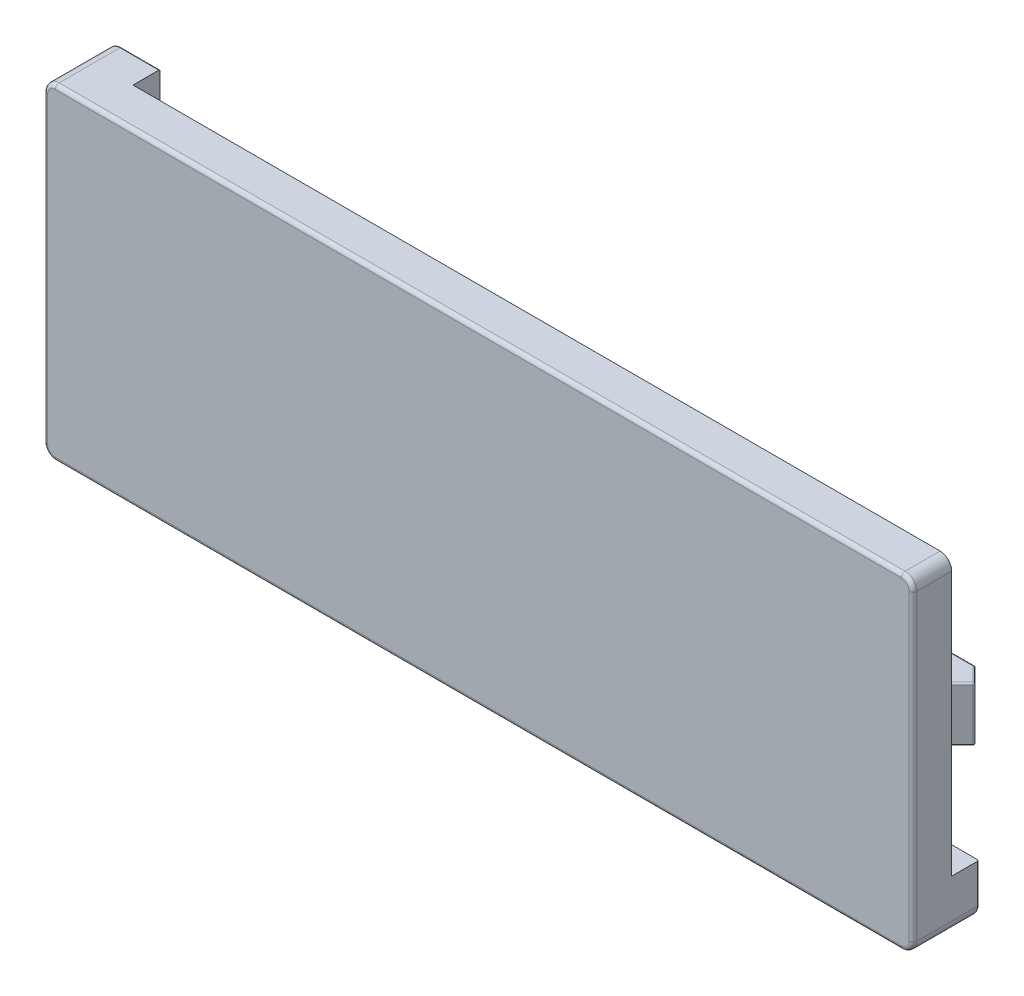
SolidWorks part; units mm, degrees
ref_plane "Front Plane" through (0, 0, 0) normal (0, 0, 1) x (1, 0, 0)
ref_plane "Top Plane" through (0, 0, 0) normal (0, 1, 0) x (1, 0, 0)
ref_plane "Right Plane" through (0, 0, 0) normal (1, 0, 0) x (0, 0, -1)
sketch "Sketch1" plane through (0, 0, 0) normal (0, 0, 1) x (1, 0, 0)
  line L1 (55.95, -21) -> (-55.95, -21)
  line L2 (55.95, -21) -> (55.95, 21)
  line L3 (55.95, 21) -> (-55.95, 21)
  line L4 (-55.95, -21) -> (-55.95, 21)
  line L5 (55.95, -21) -> (-55.95, 21) construction
  line L6 (55.95, 21) -> (-55.95, -21) construction
  point P0 (0, 0)
  dimension "D1" = 111.9
  dimension "D2" = 42
extrude "Boss-Extrude1" add sketch "Sketch1" along normal blind 5
sketch "Sketch2" plane through (0, 0, 0) normal (0, 0, -1) x (-1, 0, 0)
  line L1 (55.95, 21) -> (49.45, 21)
  line L2 (55.95, 21) -> (55.95, 14.5)
  line L3 (55.95, 14.5) -> (49.45, 14.5)
  line L4 (49.45, 21) -> (49.45, 14.5)
  line L5 (-55.95, -21) -> (-49.45, -21)
  line L6 (-55.95, -21) -> (-55.95, -14.5)
  line L7 (-55.95, -14.5) -> (-49.45, -14.5)
  line L8 (-49.45, -21) -> (-49.45, -14.5)
  dimension "D1" = 6.5
  dimension "D2" = 6.5
extrude "Boss-Extrude2" add sketch "Sketch2" along normal blind 3.5
sketch "Sketch3" plane through (0, 0, 0) normal (0, 0, -1) x (-1, 0, 0)
  line L0 (-45.45, -17) -> (51.95, -17)
  line L1 (51.95, -17) -> (51.95, 10.5)
  line L2 (51.95, 10.5) -> (45.45, 10.5)
  line L3 (45.45, 10.5) -> (45.45, 17)
  line L4 (45.45, 17) -> (-51.95, 17)
  line L5 (-51.95, 17) -> (-51.95, -10.5)
  line L6 (-51.95, -10.5) -> (-45.45, -10.5)
  line L7 (-45.45, -10.5) -> (-45.45, -17)
  line L8 (-49.45, -14.5) -> (-49.45, -21)
  line L9 (-49.45, -21) -> (55.95, -21)
  line L10 (55.95, -21) -> (55.95, 14.5)
  line L11 (55.95, 14.5) -> (49.45, 14.5)
  line L12 (49.45, 14.5) -> (49.45, 21)
  line L13 (49.45, 21) -> (-55.95, 21)
  line L14 (-55.95, 21) -> (-55.95, -14.5)
  line L15 (-55.95, -14.5) -> (-49.45, -14.5)
  line L16 (-49.45, -14.5) -> (-49.45, -21) construction
  line L17 (-49.45, -21) -> (55.95, -21) construction
  line L18 (55.95, -21) -> (55.95, 14.5) construction
  line L19 (55.95, 14.5) -> (49.45, 14.5) construction
  line L20 (49.45, 14.5) -> (49.45, 21) construction
  line L21 (49.45, 21) -> (-55.95, 21) construction
  line L22 (-55.95, 21) -> (-55.95, -14.5) construction
  line L23 (-55.95, -14.5) -> (-49.45, -14.5) construction
  line L24 (-42.45, -14) -> (48.95, -14)
  line L25 (48.95, -14) -> (48.95, 7.5)
  line L26 (48.95, 7.5) -> (42.45, 7.5)
  line L27 (42.45, 7.5) -> (42.45, 14)
  line L28 (42.45, 14) -> (-48.95, 14)
  line L29 (-48.95, 14) -> (-48.95, -7.5)
  line L30 (-48.95, -7.5) -> (-42.45, -7.5)
  line L31 (-42.45, -7.5) -> (-42.45, -14)
  dimension "D1" = 0
  dimension "D2" = 4
  dimension "D3" = 3
extrude "Cut-Extrude1" cut sketch "Sketch3" against normal blind 2
sketch "Sketch5" plane through (0, 0, 0) normal (0, 0, -1) x (-1, 0, 0)
  line L0 (-40.45, -12) -> (46.95, -12)
  line L1 (46.95, -12) -> (46.95, 5.5)
  line L2 (46.95, 5.5) -> (40.45, 5.5)
  line L3 (40.45, 5.5) -> (40.45, 12)
  line L4 (40.45, 12) -> (-46.95, 12)
  line L5 (-46.95, 12) -> (-46.95, -5.5)
  line L6 (-46.95, -5.5) -> (-40.45, -5.5)
  line L7 (-40.45, -5.5) -> (-40.45, -12)
  line L8 (-42.45, -7.5) -> (-42.45, -14)
  line L9 (-42.45, -14) -> (48.95, -14)
  line L10 (48.95, -14) -> (48.95, 7.5)
  line L11 (48.95, 7.5) -> (42.45, 7.5)
  line L12 (42.45, 7.5) -> (42.45, 14)
  line L13 (42.45, 14) -> (-48.95, 14)
  line L14 (-48.95, 14) -> (-48.95, -7.5)
  line L15 (-48.95, -7.5) -> (-42.45, -7.5)
  line L16 (-42.45, -7.5) -> (-42.45, -14)
  line L17 (-42.45, -14) -> (48.95, -14)
  line L18 (48.95, -14) -> (48.95, 7.5)
  line L19 (48.95, 7.5) -> (42.45, 7.5)
  line L20 (42.45, 7.5) -> (42.45, 14)
  line L21 (42.45, 14) -> (-48.95, 14)
  line L22 (-48.95, 14) -> (-48.95, -7.5)
  line L23 (-48.95, -7.5) -> (-42.45, -7.5)
  dimension "D1" = 0
  dimension "D2" = 2
extrude "Cut-Extrude2" cut sketch "Sketch5" against normal blind 2 contours L0 L1 L2 L3 L4 L5 L6 L7
ref_plane "Plane1" through (0, 0, 0) normal (0, -1, 0) x (-1, 0, 0)
sketch "Sketch6" plane through (0, 0, 0) normal (0, -1, 0) x (-1, 0, 0)
  line L0 (48.95, -2) -> (48.95, 0)
  line L1 (48.95, -2) -> (48.95, 0)
  line L2 (51.95, -2) -> (48.95, -2)
  line L3 (-48.95, -2) -> (-51.95, -2)
  line L4 (-48.95, -2) -> (-51.95, -2)
  line L5 (51.95, -2) -> (48.95, -2)
  line L6 (51.95, -2) -> (51.95, 0)
  line L7 (51.95, -2) -> (51.95, 0)
  line L8 (48.95, 0) -> (48.95, 7)
  line L9 (51.95, 0) -> (51.95, 3)
  line L10 (51.95, 3) -> (53.95, 5)
  line L11 (53.95, 5) -> (51.95, 7)
  line L12 (51.95, 7) -> (48.95, 7)
  line L14 (45.95, 7) -> (52.95, 7) construction
  point P9 (51.95, 10)
  point P11 (54.45, 7.5)
  point P12 (54.45, 7.5)
  point P13 (51.2786, 10)
  dimension "D1" = 3
  dimension "D2" = 135
  dimension "D3" = 2
  dimension "D4" = 0
  dimension "D5" = 2
  dimension "D6" = 135
extrude "Boss-Extrude3" add sketch "Sketch6" along normal mid plane 7 contours L11 L12 L8 L1 L5 L7 L9 L10
fillet "Fillet1" radius 0.2 9 edges at (-51.95, 3.5, -1.5) (-48.95, 3.5, -3.5) (-50.45, 3.5, -7) (-52.95, 3.5, -4) (-52.95, 3.5, -6) (-48.95, 0, -7) (-51.95, 0, -7) (-51.95, 0, -3) (-53.95, 0, -5)
ref_plane "Plane2" through (0, 0, 0) normal (-1, 0, 0) x (0, 0, 1)
mirror "Mirror1" about plane through (0, 0, 0) normal (-1, 0, 0) of "Fillet1", "Boss-Extrude3"
fillet "Fillet2" radius 1.5 4 edges at (-55.95, -21, 2.5) (-55.95, 21, 0.75) (55.95, -21, 0.75) (55.95, 21, 2.5)
fillet "Fillet3" radius 0.5 8 edges at (-55.5107, 20.5607, 5) (0, 21, 5) (55.5107, 20.5607, 5) (55.95, 0, 5) (55.5107, -20.5607, 5) (0, -21, 5) (-55.5107, -20.5607, 5) (-55.95, 0, 5)
fillet "Fillet4" radius 0.2 41 edges at (43.7, -5.5, 2) (46.95, 3.25, 2) (3.25, 12, 2) (-40.45, 8.75, 2) (-43.7, 5.5, 2) (-46.95, -3.25, 2) (-3.25, -12, 2) (40.45, -8.75, 2) (3.25, 17, 2) (-45.45, 13.75, 2) (-48.7, 10.5, 2) (-51.95, 7, 2) (-50.45, 3.5, 2) (-48.95, 5.5, 2) (-45.7, 7.5, 2) (-42.45, 10.75, 2) (3.25, 14, 2) (48.95, 8.75, 2) (50.45, 3.5, 2) (51.95, 10.25, 2) (48.95, -5.5, 2) (45.7, -7.5, 2) (42.45, -10.75, 2) (-3.25, -14, 2) (-48.95, -8.75, 2) (-50.45, -3.5, 2) (-51.95, -10.25, 2) (-3.25, -17, 2) (45.45, -13.75, 2) (48.7, -10.5, 2) (51.95, -7, 2) (50.45, -3.5, 2) (51.95, -3.5, 1) (48.95, -3.5, 1) (51.95, 3.5, 1) (48.95, 3.5, 1) (-48.95, -3.5, 1) (-51.95, -3.5, 1) (-48.95, 3.5, 1) (-51.95, 3.5, 1) (-51.95, -17, 1)
fillet "Fillet5" radius 0.2 18 edges at (51.95, -3.5, -1.4586) (51.9652, -3.5, -2.9937) (52.9086, -3.5, -3.9586) (53.8672, -3.5, -5) (52.9086, -3.5, -6.0414) (51.9437, -3.5, -6.9848) (50.5086, -3.5, -7) (49.0086, -3.5, -6.9414) (-51.95, -3.5, -1.4586) (-51.9652, -3.5, -2.9937) (-52.9086, -3.5, -3.9586) (-53.8672, -3.5, -5) (-52.9086, -3.5, -6.0414) (-51.9437, -3.5, -6.9848) (-50.5086, -3.5, -7) (-49.0086, -3.5, -6.9414) (48.95, -3.5, -3.4) (-48.95, -3.5, -3.4)
fillet "Fillet6" radius 0.2 6 edges at (-51.95, 21, -3.5) (-55.5107, 20.5607, -3.5) (51.95, -21, -3.5) (55.5107, -20.5607, -3.5) (-55.95, 17, -3.5) (55.95, -17, -3.5)
